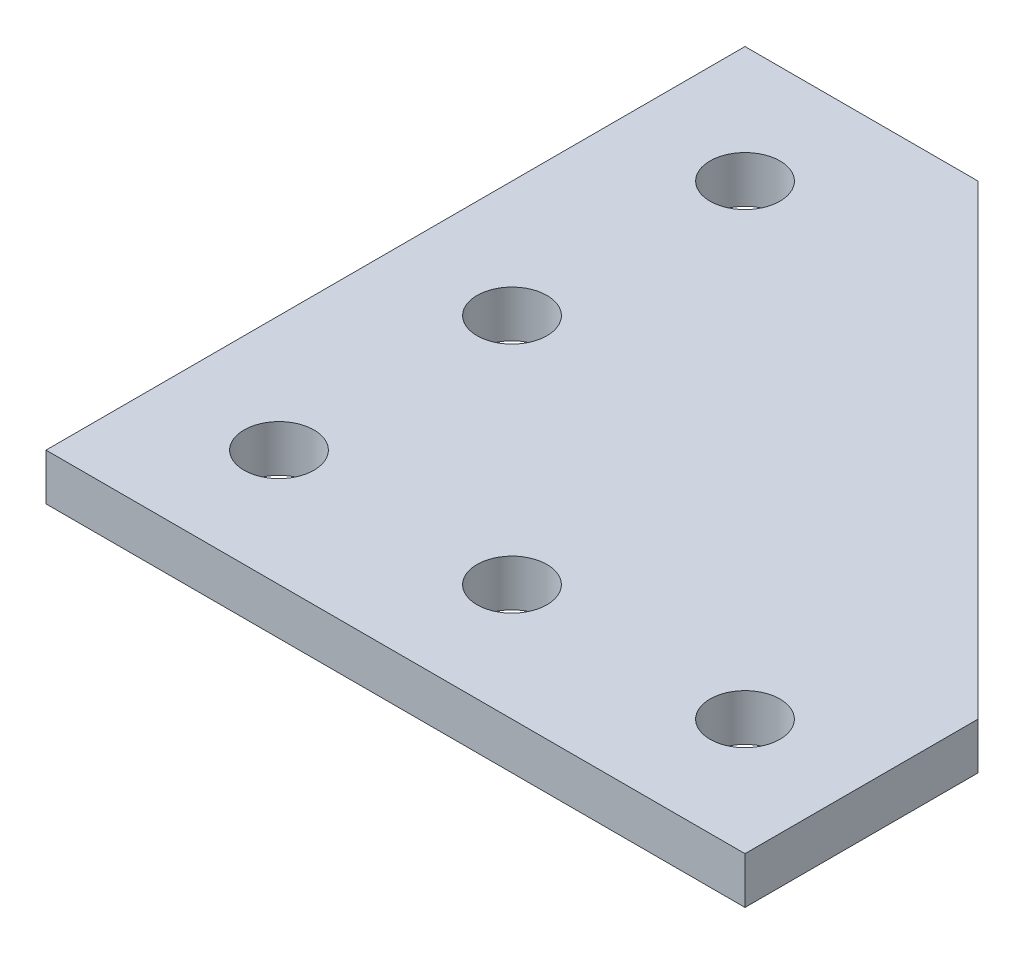
SolidWorks part; units mm, degrees
ref_plane "Front Plane" through (0, 0, 0) normal (0, 0, 1) x (1, 0, 0)
ref_plane "Top Plane" through (0, 0, 0) normal (0, 1, 0) x (1, 0, 0)
ref_plane "Right Plane" through (0, 0, 0) normal (1, 0, 0) x (0, 0, -1)
sketch "Sketch2" plane through (0, 0, 0) normal (0, 1, 0) x (1, 0, 0)
  line L0 (0, 0) -> (0, 60)
  line L1 (0, 60) -> (20, 60)
  line L2 (20, 60) -> (60, 20)
  line L3 (60, 20) -> (60, 0)
  line L4 (60, 0) -> (0, 0)
  dimension "D1" = 20
  dimension "D2" = 60
extrude "Boss-Extrude1" add sketch "Sketch2" along normal blind 4
sketch "Sketch3" plane through (0, 4, 0) normal (0, 1, 0) x (1, 0, 0)
  line L0 (10, 60) -> (10, 0) construction
  line L1 (20, 60) -> (0, 60) construction
  line L2 (0, 0) -> (60, 0) construction
  line L3 (0, 0) -> (40, 40) construction
  line L4 (60, 20) -> (20, 60) construction
  line L5 (60, 10) -> (0, 10) construction
  line L6 (60, 0) -> (60, 20) construction
  line L7 (0, 60) -> (0, 0) construction
  circle A2 centre (10, 10) radius 3
  circle A3 centre (30, 10) radius 3
  circle A4 centre (50, 10) radius 3
  circle A8 centre (10, 50) radius 3
  circle A9 centre (10, 30) radius 3
  dimension "D1" = 3
  dimension "D2" = 6
  dimension "D3" = 20
extrude "Cut-Extrude1" cut sketch "Sketch3" against normal through all
